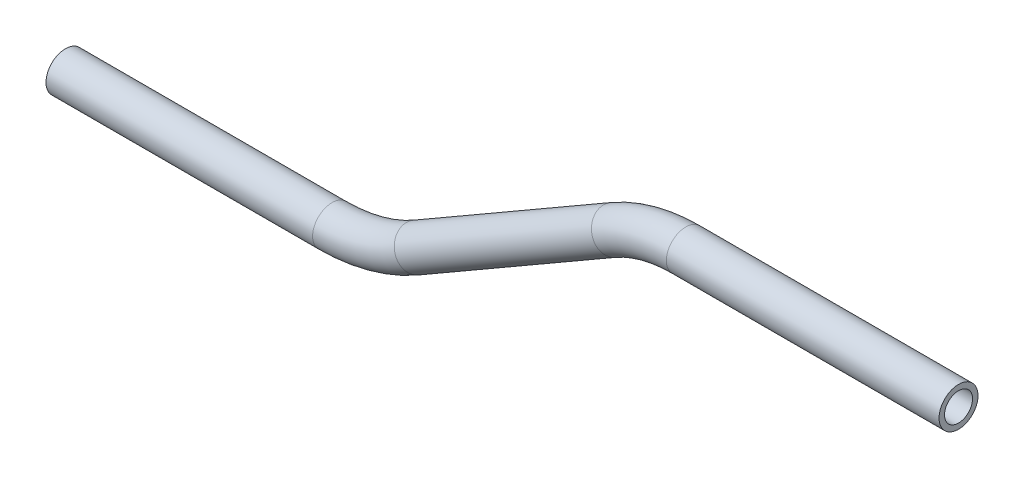
SolidWorks part; units mm, degrees
material "AISI 316 Stainless Steel Sheet (SS)"
ref_plane "Front Plane" through (0, 0, 0) normal (0, 0, 1) x (1, 0, 0)
ref_plane "Top Plane" through (0, 0, 0) normal (0, 1, 0) x (1, 0, 0)
ref_plane "Right Plane" through (0, 0, 0) normal (1, 0, 0) x (0, 0, -1)
sketch "Sketch1" plane through (0, 0, 0) normal (0, 0, 1) x (1, 0, 0)
  line L0 (0, 0) -> (44.46, 0)
  line L1 (-11.8306, -3.17) -> (-43.9793, -21.731)
  line L2 (-57.672, -25.4) -> (-101.1341, -25.4)
  line L3 (44.46, 0) -> (-16.7409, 0) construction
  line L4 (-101.1341, -25.4) -> (-45.2016, -25.4) construction
  line L5 (4.6446, 6.342) -> (-46.7361, -23.3227) construction
  arc A0 (0, 0) -> (-11.8306, -3.17) centre (0, -23.6612) ccw
  arc A1 (-43.9793, -21.731) -> (-57.672, -25.4) centre (-57.672, 1.9855) cw
  point P8 (-50.3341, -25.4)
  point P14 (-6.34, 0)
  point P15 (0, 0)
  point P16 (0, 0)
  dimension "D1" = 30
  dimension "D2" = 30
  dimension "D3" = 50.8
  dimension "D4" = 50.8
  dimension "D5" = 50.8
ref_plane "Plane1" through (44.46, 0, 0) normal (1, 0, 0) x (0, 0, -1)
sketch "Sketch2" plane through (44.46, 0, 0) normal (1, 0, 0) x (0, 0, -1)
  circle A0 centre (0, 0) radius 3.175
  circle A1 centre (0, 0) radius 2.286
  dimension "D1" = 4.572
  dimension "D2" = 6.35
sweep "Sweep1" add profiles "Sketch2" path "Sketch1"
